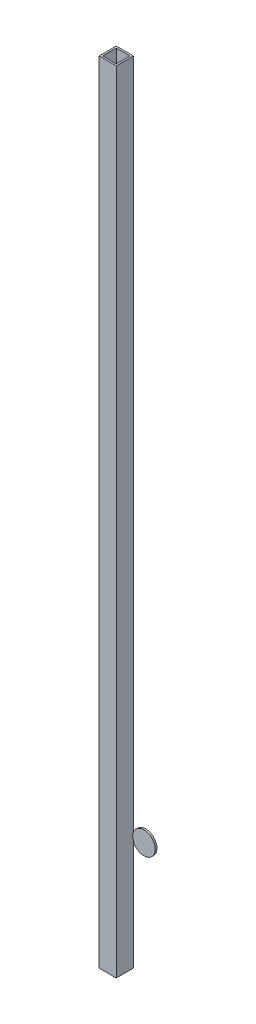
SolidWorks part; units mm, degrees
ref_plane "Front Plane" through (0, 0, 0) normal (0, 0, 1) x (1, 0, 0)
ref_plane "Top Plane" through (0, 0, 0) normal (0, 1, 0) x (1, 0, 0)
ref_plane "Right Plane" through (0, 0, 0) normal (1, 0, 0) x (0, 0, -1)
sketch "Sketch2" plane through (0, 0, 0) normal (0, 0, 1) x (1, 0, 0)
  line L0 (0, 0) -> (0, 1168.4)
  dimension "D1" = 1168.4
other "Extrusion 1X1X0.1(1)"
ref_plane "Plane3" through (0, 0, 0) normal (0, 1, 0) x (-1, 0, 0)
sketch "Sketch1" plane through (0, 0, 0) normal (0, 1, 0) x (-1, 0, 0)
  line L0 (22.86, 2.54) -> (22.86, 22.86)
  line L1 (0, 0) -> (25.4, 0)
  line L2 (0, 0) -> (0, 25.4)
  line L3 (0, 25.4) -> (25.4, 25.4)
  line L4 (25.4, 0) -> (25.4, 25.4)
  line L5 (2.54, 22.86) -> (22.86, 22.86)
  line L6 (2.54, 2.54) -> (2.54, 22.86)
  line L7 (2.54, 2.54) -> (22.86, 2.54)
  line L8 (12.7, 0) -> (12.7, 25.4) construction
  point P8 (25.4, 12.7)
  point P9 (0, 25.4)
  point P10 (25.4, 25.4)
  point P11 (0, 12.7)
  point P12 (12.7, 0)
  point P13 (0, 0)
  point P15 (25.4, 0)
  point P17 (12.7, 12.7)
  point P18 (0, 0)
  dimension "D1" = 25.4
  dimension "D2" = 25.4
  dimension "D3" = 2.54
sketch "Sketch3" plane through (0, -24.7237, 0) normal (0, 0, 1) x (1, 0, 0)
  circle A0 centre (16.832, 194.2503) radius 16.6423
  point P2 (16.832, 194.2503)
extrude "Boss-Extrude1" add sketch "Sketch3" along normal mid plane 2.54 separate body
